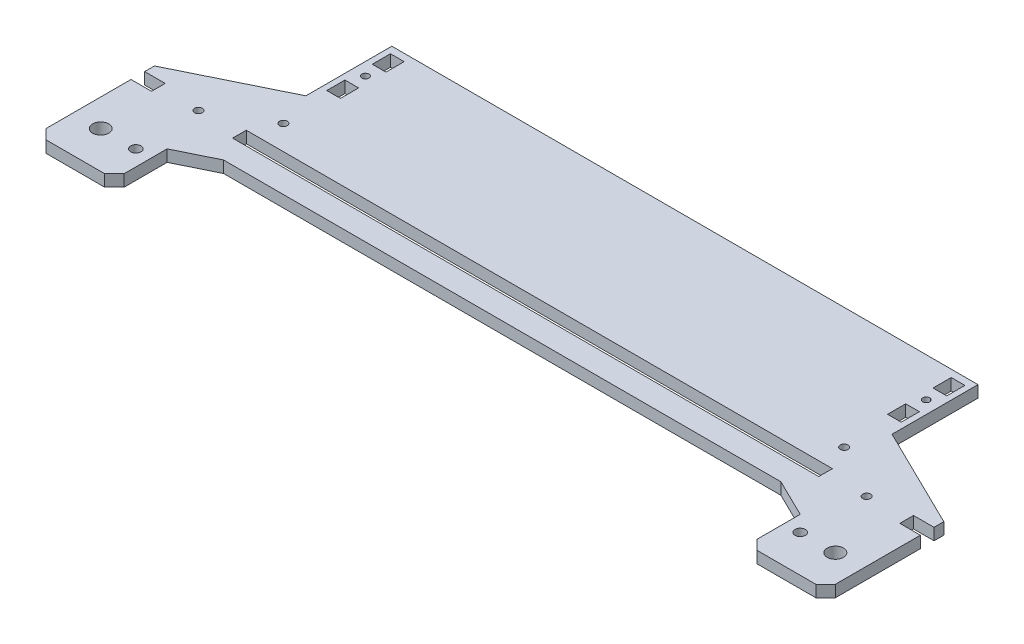
SolidWorks part; units mm, degrees
ref_plane "Plan de face" through (0, 0, 0) normal (0, 0, 1) x (1, 0, 0)
ref_plane "Plan de dessus" through (0, 0, 0) normal (0, 1, 0) x (1, 0, 0)
ref_plane "Plan de droite" through (0, 0, 0) normal (1, 0, 0) x (0, 0, -1)
sketch "Esquisse1" plane through (0, 0, 0) normal (0, 1, 0) x (1, 0, 0)
  line L0 (-150, 0) -> (0, 0) construction
  line L1 (-150, 0) -> (-202, -25.5)
  line L2 (-202, -25.5) -> (-202, -30.5)
  line L3 (-202, -30.5) -> (-191.5, -30.5)
  line L4 (-191.5, -30.5) -> (-191.5, -37.5)
  line L5 (-191.5, -37.5) -> (-202, -37.5)
  line L6 (-202, -37.5) -> (-202, -86)
  line L7 (-202, -86) -> (-162, -86)
  line L8 (-162, -86) -> (-162, -59)
  line L9 (-162, -59) -> (-142.6275, -49.5)
  line L10 (-142.6275, -49.5) -> (0, -49.5)
  line L11 (0, -49.5) -> (0, -37.5)
  line L12 (0, -37.5) -> (-150, -37.5)
  line L13 (-150, -37.5) -> (-150, -30.5)
  line L14 (-150, -30.5) -> (0, -30.5)
  line L15 (0, -30.5) -> (0, 0)
  line L16 (-192, -34) -> (-150, -34) construction
  line L17 (-150, 0) -> (-150, 44)
  line L18 (-150, 44) -> (0, 44)
  line L19 (0, 44) -> (0, 0)
  line L20 (-188, -67) -> (-170, -67) construction
  line L21 (-143.5, 0) -> (-143.5, -30.5) construction
  line L22 (0, 0) -> (0, 59.5738) construction
  line L23 (-150, -37) -> (-150, -31) construction
  line L24 (-192, -37) -> (-192, -31) construction
  circle A0 centre (-188, -67) radius 4.15
  circle A1 centre (-171, -34) radius 2
  circle A2 centre (-170, -67) radius 2.65
  circle A3 centre (-143.5, -18) radius 2
  dimension "D10" = 8.3
  dimension "D16" = 4
  dimension "D18" = 5.3
  dimension "D2" = 86
  dimension "D3" = 25.5
  dimension "D4" = 150
  dimension "D5" = 7
  dimension "D6" = 5
  dimension "D7" = 10.5
  dimension "D8" = 40
  dimension "D9" = 14
  dimension "D11" = 19
  dimension "D12" = 404
  dimension "D13" = 27
  dimension "D14" = 12
  dimension "D15" = 7
  dimension "D17" = 44
  dimension "D19" = 18
  dimension "D20" = 6.5
  dimension "D22" = 12.5
extrude "Boss.-Extru.1" add sketch "Esquisse1" along normal blind 6
chamfer "Chanfrein1" distance 5 angle 45 2 edges at (-162, 3, 86) (-202, 3, 86)
sketch "Esquisse3" plane through (0, 6, 0) normal (0, 1, 0) x (1, 0, 0)
  line L0 (-143.5, 44) -> (-143.5, -30.5) construction
  line L1 (0, 44) -> (-150, 44) construction
  line L2 (-150, -30.5) -> (0, -30.5) construction
  line L3 (-150, 44) -> (-150, 0) construction
  line B0 (-140, 40.3) -> (-140, 31)
  line B1 (-140, 40.3) -> (-147, 40.3)
  line B2 (-147, 40.3) -> (-147, 31)
  line B3 (-140, 31) -> (-147, 31)
  line B4 (-140, 17) -> (-147, 17)
  line B5 (-147, 7.7) -> (-147, 17)
  line B6 (-140, 7.7) -> (-147, 7.7)
  line B7 (-140, 7.7) -> (-140, 17)
  circle B8 centre (-143.5, 24) radius 1.8
  dimension "D1" = 6.5
  dimension "D2" = 20
sketch_block_instance "Bloc-attache-femelle-1"
sketch_block "Bloc-attache-femelle" parameters "D1"=3.6, "D2"=9.3, "D3"=7, "D4"=7
extrude "Enlèv. mat.-Extru.1" cut sketch "Esquisse3" against normal blind 6
mirror "Symétrie1" about plane through (0, 6, 30.5) normal (-1, 0, 0) of bodies 103 101
equation "\"W\"= \"W@Prusa i4.2.sldasm\""
equation "\"D12@Esquisse1\"=\"W\"+104"
equation "\"D4@Esquisse1\"=\"W\"/2"
